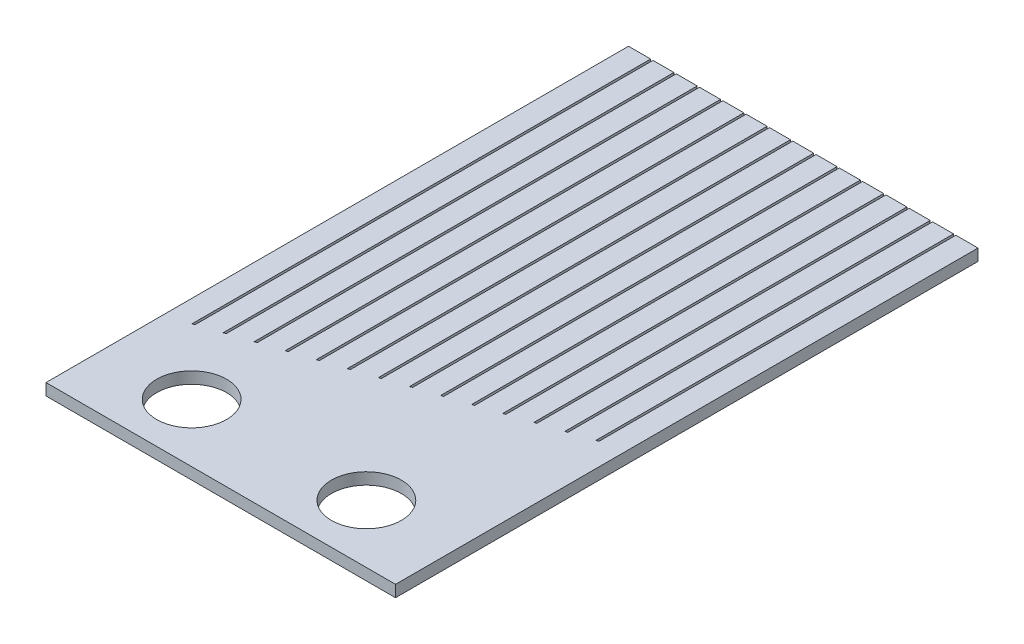
SolidWorks part; units mm, degrees
material "1023 Carbon Steel Sheet (SS)"
ref_plane "Front" through (0, 0, 0) normal (0, 0, 1) x (1, 0, 0)
ref_plane "Top" through (0, 0, 0) normal (0, 1, 0) x (1, 0, 0)
ref_plane "Right" through (0, 0, 0) normal (1, 0, 0) x (0, 0, -1)
sketch "Sketch1" plane through (0, 0, 0) normal (0, 1, 0) x (1, 0, 0)
  line L0 (-7.5, -7.5) -> (7.5, -2.5)
  line L1 (-7.5, -12.5) -> (7.5, -12.5)
  line L2 (-7.5, -12.5) -> (-7.5, 12.5)
  line L3 (-7.5, 12.5) -> (7.5, 12.5)
  line L4 (7.5, -12.5) -> (7.5, 12.5)
  line L5 (-7.5, -12.5) -> (7.5, 12.5) construction
  line L6 (-7.5, 12.5) -> (7.5, -12.5) construction
  line L7 (-6.55, -7.1833) -> (-6.55, 12.5)
  line L8 (-6.45, -7.15) -> (-6.45, 12.5)
  line L9 (-5.55, -6.85) -> (-5.55, 12.5)
  line L10 (-5.45, -6.8167) -> (-5.45, 12.5)
  line L11 (-4.55, -6.5167) -> (-4.55, 12.5)
  line L12 (-4.45, -6.4833) -> (-4.45, 12.5)
  line L13 (-3.55, -6.1833) -> (-3.55, 12.5)
  line L14 (-3.45, -6.15) -> (-3.45, 12.5)
  line L15 (-2.55, -5.85) -> (-2.55, 12.5)
  line L16 (-2.45, -5.8167) -> (-2.45, 12.5)
  line L17 (-1.55, -5.5167) -> (-1.55, 12.5)
  line L18 (-1.45, -5.4833) -> (-1.45, 12.5)
  line L19 (-0.55, -5.1833) -> (-0.55, 12.5)
  line L20 (0.45, -4.85) -> (0.45, 12.5)
  line L21 (1.45, -4.5167) -> (1.45, 12.5)
  line L22 (2.45, -4.1833) -> (2.45, 12.5)
  line L23 (1.55, -4.4833) -> (1.55, 12.5)
  line L24 (2.55, -4.15) -> (2.55, 12.5)
  line L25 (0.55, -4.8167) -> (0.55, 12.5)
  line L26 (-0.45, -5.15) -> (-0.45, 12.5)
  line L27 (3.45, -3.85) -> (3.45, 12.5)
  line L28 (4.45, 12.5) -> (4.45, -3.5167)
  line L29 (5.45, 12.5) -> (5.45, -3.1833)
  line L30 (5.55, 12.5) -> (5.55, -3.15)
  line L31 (4.55, 12.5) -> (4.55, -3.4833)
  line L32 (3.55, 12.5) -> (3.55, -3.8167)
  line L33 (6.45, 12.5) -> (6.45, -2.85)
  line L34 (6.55, 12.5) -> (6.55, -2.8167)
  circle A0 centre (-3.75, -10) radius 1.5
  circle A1 centre (3.75, -10) radius 1.5
  point P0 (0, 0)
  dimension "D33" = 3
  dimension "D36" = 2
  dimension "D1" = 15
  dimension "D2" = 25
  dimension "D3" = 5
  dimension "D4" = 10
  dimension "D5" = 0.95
  dimension "D6" = 0.1
  dimension "D7" = 0.9
  dimension "D8" = 0.1
  dimension "D9" = 0.9
  dimension "D10" = 0.1
  dimension "D11" = 0.9
  dimension "D12" = 0.1
  dimension "D13" = 0.9
  dimension "D14" = 0.1
  dimension "D15" = 0.9
  dimension "D16" = 0.1
  dimension "D17" = 0.9
  dimension "D18" = 0.1
  dimension "D19" = 0.9
  dimension "D20" = 0.1
  dimension "D21" = 0.9
  dimension "D22" = 0.1
  dimension "D23" = 0.9
  dimension "D24" = 0.1
  dimension "D25" = 0.9
  dimension "D26" = 0.1
  dimension "D27" = 0.9
  dimension "D28" = 0.1
  dimension "D29" = 0.9
  dimension "D30" = 0.1
  dimension "D31" = 0.9
  dimension "D32" = 0.1
  dimension "D34" = 2.5
  dimension "D35" = 3.75
extrude "Boss-Extrude1" add sketch "Sketch1" along normal blind 0.5 contours L1 L4 L0 L2 A1 A0 | L3 L34 L0 L4 | L33 L3 L30 L0 | L3 L31 L0 L29 | L3 L32 L0 L28 | L0 L27 L3 L24 | L23 L0 L22 L3 | L25 L0 L21 L3 | L26 L0 L20 L3 | L0 L19 L3 L18 | L0 L17 L3 L16 | L0 L15 L3 L14 | L0 L13 L3 L12 | L0 L11 L3 L10 | L0 L9 L3 L8 | L0 L7 L3 L2
